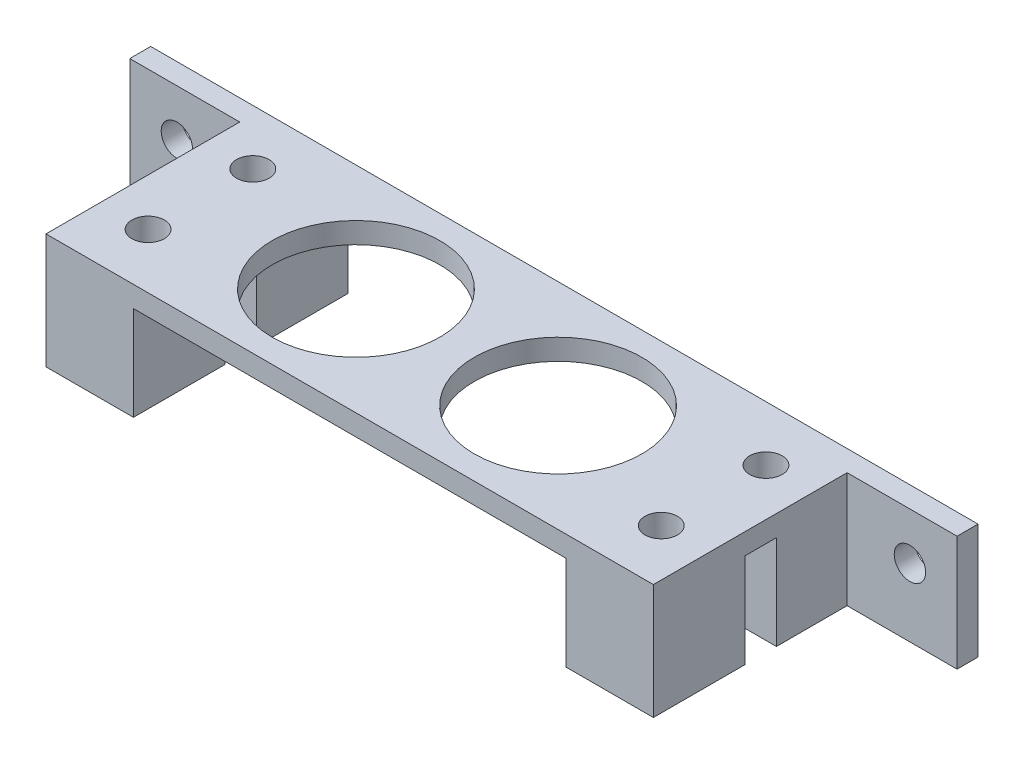
SolidWorks part; units mm, degrees
ref_plane "Front Plane" through (0, 0, 0) normal (0, 0, 1) x (1, 0, 0)
ref_plane "Top Plane" through (0, 0, 0) normal (0, 1, 0) x (1, 0, 0)
ref_plane "Right Plane" through (0, 0, 0) normal (1, 0, 0) x (0, 0, -1)
sketch "Sketch2" plane through (0, 0, 0) normal (0, 1, 0) x (1, 0, 0)
  line L0 (-24.5, 5) -> (-24.5, -5) construction
  line L1 (-29, 10.25) -> (29, 10.25)
  line L2 (-29, 10.25) -> (-29, -10.25)
  line L3 (-29, -10.25) -> (29, -10.25)
  line L4 (29, 10.25) -> (29, -10.25)
  line L5 (-29, 10.25) -> (29, -10.25) construction
  line L6 (-29, -10.25) -> (29, 10.25) construction
  line L7 (-24.5, -5) -> (24.5, -5) construction
  line L8 (24.5, -5) -> (24.5, 5) construction
  line L9 (24.5, 5) -> (-24.5, 5) construction
  line L10 (-20.65, 10.25) -> (-20.65, -10.25) construction
  line L15 (20.65, 10.25) -> (20.65, -10.25) construction
  line L16 (-20.65, 0) -> (20.65, 0) construction
  circle A0 centre (-9.65, 0) radius 8
  circle A1 centre (-24.5, 5) radius 1.55
  circle A2 centre (-24.5, -5) radius 1.55
  circle A3 centre (24.5, 5) radius 1.55
  circle A4 centre (24.5, -5) radius 1.55
  circle A5 centre (9.65, 0) radius 8
  point P0 (0, 0)
  point P16 (-24.5, 0)
  point P17 (0, 5)
  point P27 (0, 0)
  dimension "D1" = 16
  dimension "D2" = 3.1
  dimension "D9" = 41.3
  dimension "D10" = 11
  dimension "D3" = 4.5
  dimension "D4" = 10
  dimension "D5" = 49
  dimension "D6" = 20.5
  dimension "D7" = 11
extrude "Boss-Extrude1" add sketch "Sketch2" along normal blind 2
sketch "Sketch3" plane through (0, 0, 0) normal (0, -1, 0) x (1, 0, 0)
  line L0 (-20.65, 10.25) -> (-20.65, -10.25)
  line L1 (-29, 10.25) -> (29, 10.25) construction
  line L2 (-29, -10.25) -> (29, -10.25) construction
  line L3 (-20.65, -10.25) -> (-29, -10.25)
  line L4 (-29, -10.25) -> (-29, 10.25)
  line L5 (-29, 10.25) -> (-20.65, 10.25)
  line L6 (20.65, 10.25) -> (20.65, -10.25)
  line L7 (20.65, -10.25) -> (29, -10.25)
  line L8 (29, -10.25) -> (29, 10.25)
  line L9 (29, 10.25) -> (20.65, 10.25)
  line L10 (-29, 10.25) -> (29, 10.25) construction
  line L12 (-29, 1.5) -> (-20.65, 1.5)
  line L13 (-29, 1.5) -> (-29, -1.5)
  line L14 (-29, -1.5) -> (-20.65, -1.5)
  line L15 (-20.65, 1.5) -> (-20.65, -1.5)
  line L16 (20.65, 1.5) -> (29, 1.5)
  line L17 (20.65, 1.5) -> (20.65, -1.5)
  line L18 (20.65, -1.5) -> (29, -1.5)
  line L19 (29, 1.5) -> (29, -1.5)
  circle A0 centre (-24.5, -5) radius 1.55
  circle A1 centre (-24.5, 5) radius 1.55
  circle A2 centre (24.5, -5) radius 1.55
  circle A3 centre (24.5, 5) radius 1.55
  point P43 (20.65, 0)
  point P44 (-20.65, 0)
  circle M5 centre (24.5, 5) radius 1.55
  circle M6 centre (24.5, -5) radius 1.55
  circle M7 centre (-24.5, 5) radius 1.55
  circle M8 centre (-24.5, -5) radius 1.55
  line M13 (29, -10.25) -> (29, 10.25)
  line M14 (29, 10.25) -> (-29, 10.25)
  line M15 (-29, 10.25) -> (-29, -10.25)
  line M16 (-29, -10.25) -> (29, -10.25)
  dimension "D1" = 3
extrude "Boss-Extrude2" add sketch "Sketch3" along normal blind 9 contours L12 L0 M15 M14 M7 | L14 L0 M15 M16 M8 | L6 L16 L8 M14 M5 | L18 L6 M16 M13 M6
sketch "Sketch4" plane through (0, 0, -10.25) normal (0, 0, -1) x (-1, 0, 0)
  line L0 (35, -2.5) -> (-35, -2.5) construction
  line L1 (39.5, 2) -> (-39.5, 2)
  line L2 (39.5, 2) -> (39.5, -9)
  line L3 (39.5, -9) -> (-39.5, -9)
  line L4 (-39.5, 2) -> (-39.5, -9)
  line L5 (29, 2) -> (29, -9) construction
  line L6 (-20.65, -9) -> (-29, -9) construction
  line L7 (20.65, -9) -> (20.65, 0)
  line L8 (20.65, 0) -> (-20.65, 0)
  line L9 (-20.65, -9) -> (-20.65, 0) construction
  line L10 (20.65, 0) -> (-20.65, 0) construction
  line L11 (-20.65, 0) -> (-20.65, -9)
  line L12 (29, 2) -> (29, -9)
  line L13 (-29, 2) -> (-29, -9)
  circle A0 centre (35, -2.5) radius 1.5
  circle A1 centre (-35, -2.5) radius 1.5
  point P6 (0, 2)
  point P7 (0, -2.5)
  dimension "D1" = 3
  dimension "D2" = 6
  dimension "D3" = 4.5
  dimension "D4" = 4.5
extrude "Boss-Extrude3" add sketch "Sketch4" against normal blind 2
